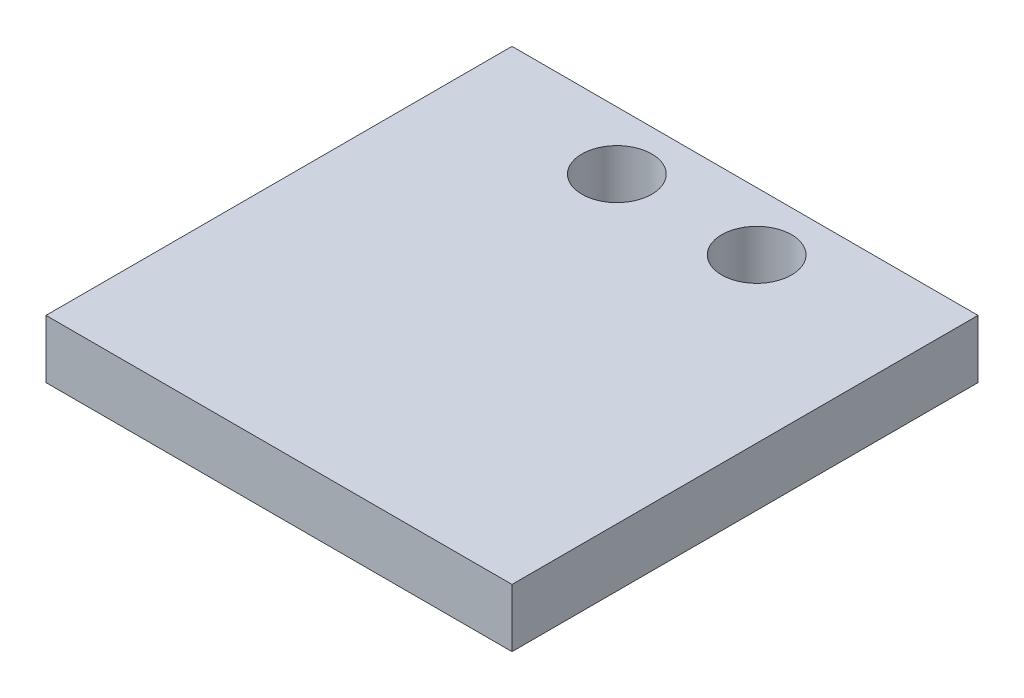
SolidWorks part; units mm, degrees
ref_plane "Front Plane" through (0, 0, 0) normal (0, 0, 1) x (1, 0, 0)
ref_plane "Top Plane" through (0, 0, 0) normal (0, 1, 0) x (1, 0, 0)
ref_plane "Right Plane" through (0, 0, 0) normal (1, 0, 0) x (0, 0, -1)
sketch "Sketch1" plane through (0, 0, 0) normal (0, 1, 0) x (1, 0, 0)
  line L1 (-10, 10) -> (10, 10)
  line L2 (-10, 10) -> (-10, -10)
  line L3 (-10, -10) -> (10, -10)
  line L4 (10, 10) -> (10, -10)
  line L5 (-10, 10) -> (10, -10) construction
  line L6 (-10, -10) -> (10, 10) construction
  circle A0 centre (-3, 7.5) radius 1.5
  circle A1 centre (3, 7.5) radius 1.5
  point P0 (0, 0)
  point P12 (1.9663, 7.4849)
  dimension "D3" = 3
  dimension "D4" = 3
  dimension "D1" = 20
  dimension "D2" = 20
  dimension "D7" = 6
  dimension "D8" = 2.5
extrude "Boss-Extrude1" add sketch "Sketch1" along normal blind 2.5
